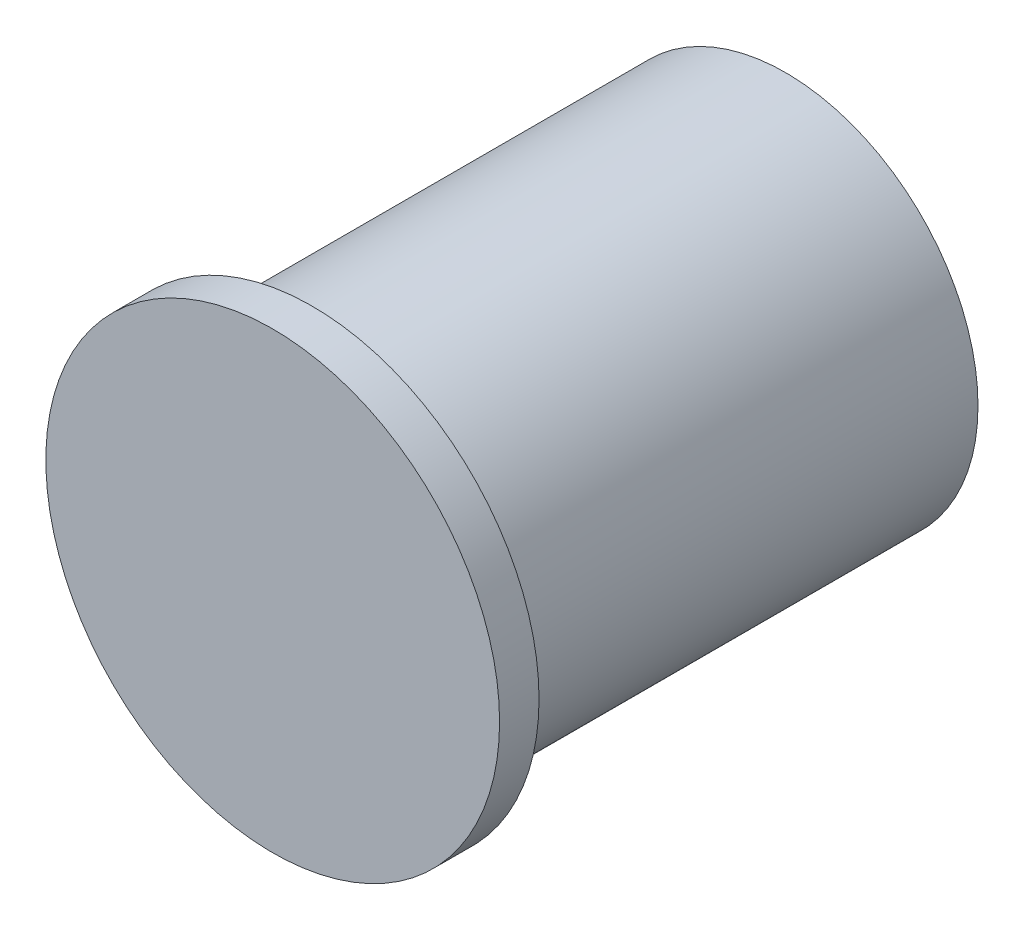
SolidWorks part; units mm, degrees
ref_plane "Front Plane" through (0, 0, 0) normal (0, 0, 1) x (1, 0, 0)
ref_plane "Top Plane" through (0, 0, 0) normal (0, 1, 0) x (1, 0, 0)
ref_plane "Right Plane" through (0, 0, 0) normal (1, 0, 0) x (0, 0, -1)
sketch "Sketch1" plane through (0, 0, 0) normal (0, 0, 1) x (1, 0, 0)
  circle A0 centre (0, 0) radius 9.75
  dimension "D1" = 19.5
extrude "Boss-Extrude1" add sketch "Sketch1" along normal blind 24
sketch "Sketch3" plane through (0, 0, 24) normal (0, 0, 1) x (1, 0, 0)
  circle A0 centre (0, 0) radius 11.5
  dimension "D1" = 23
extrude "Boss-Extrude2" add sketch "Sketch3" along normal blind 2
sketch "Sketch4" plane through (0, 0, 0) normal (0, 0, -1) x (-1, 0, 0)
  circle A0 centre (0, 0) radius 8
  circle A1 centre (0, 0) radius 9
  dimension "D1" = 16
  dimension "D2" = 18
extrude "Cut-Extrude1" cut sketch "Sketch4" against normal blind 2
